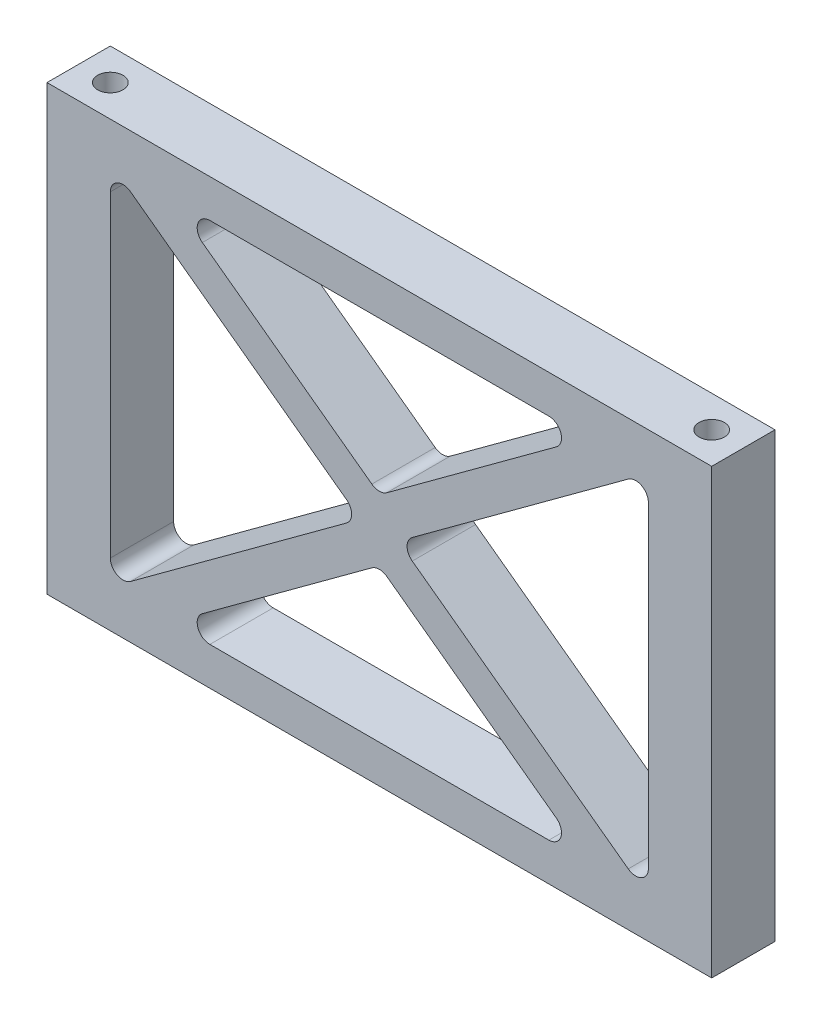
SolidWorks part; units mm, degrees
ref_plane "Ebene vorne" through (0, 0, 0) normal (0, 0, 1) x (1, 0, 0)
ref_plane "Ebene oben" through (0, 0, 0) normal (0, 1, 0) x (1, 0, 0)
ref_plane "Ebene rechts" through (0, 0, 0) normal (1, 0, 0) x (0, 0, -1)
sketch "Skizze1" plane through (0, 0, 0) normal (0, 0, 1) x (1, 0, 0)
  line L1 (0, 0) -> (105, 0)
  line L2 (0, 0) -> (0, 70)
  line L3 (0, 70) -> (105, 70)
  line L4 (105, 0) -> (105, 70)
  dimension "D1" = 105
  dimension "D2" = 70
extrude "Aufsatz-Linear austragen1" add sketch "Skizze1" along normal blind 10
sketch "Skizze2" plane through (0, 0, 10) normal (0, 0, 1) x (1, 0, 0)
  line L0 (10, 60.0503) -> (10, 9.9497)
  line L1 (52.5, 51.6277) -> (52.5, -7.4804) construction
  line L2 (13.1837, 61.6625) -> (47.3016, 36.6121)
  line L4 (51.3163, 40.7293) -> (24.5418, 60.3879)
  line L5 (25.7255, 64) -> (79.2745, 64)
  line L6 (105, 70) -> (0, 70) construction
  line L8 (0, 70) -> (0, 0) construction
  line L9 (-2.0593, 35) -> (95.2495, 35) construction
  line L10 (25.7255, 6) -> (79.2745, 6)
  line L11 (51.3163, 29.2707) -> (24.5418, 9.6121)
  line L12 (13.1837, 8.3375) -> (47.3016, 33.3879)
  line L13 (53.6837, 40.7293) -> (80.4582, 60.3879)
  line L14 (53.6837, 29.2707) -> (80.4582, 9.6121)
  line L15 (95, 60.0503) -> (95, 9.9497)
  line L16 (91.8163, 8.3375) -> (57.6984, 33.3879)
  line L17 (91.8163, 61.6625) -> (57.6984, 36.6121)
  line L18 (105, 0) -> (105, 70) construction
  arc A0 (95, 9.9497) -> (91.8163, 8.3375) centre (93, 9.9497) cw
  arc A1 (95, 60.0503) -> (91.8163, 61.6625) centre (93, 60.0503) ccw
  arc A2 (57.6984, 33.3879) -> (57.6984, 36.6121) centre (58.882, 35) cw
  arc A3 (80.4582, 9.6121) -> (79.2745, 6) centre (79.2745, 8) cw
  arc A4 (25.7255, 6) -> (24.5418, 9.6121) centre (25.7255, 8) cw
  arc A5 (51.3163, 29.2707) -> (53.6837, 29.2707) centre (52.5, 27.6586) cw
  arc A6 (80.4582, 60.3879) -> (79.2745, 64) centre (79.2745, 62) ccw
  arc A7 (51.3163, 40.7293) -> (53.6837, 40.7293) centre (52.5, 42.3414) ccw
  arc A8 (24.5418, 60.3879) -> (25.7255, 64) centre (25.7255, 62) cw
  arc A9 (47.3016, 36.6121) -> (47.3016, 33.3879) centre (46.118, 35) cw
  arc A10 (13.1837, 8.3375) -> (10, 9.9497) centre (12, 9.9497) cw
  arc A11 (10, 60.0503) -> (13.1837, 61.6625) centre (12, 60.0503) cw
  point P19 (10, 35)
  point P20 (52.5, 64)
  point P21 (52.5, 6)
  point P30 (95, 6)
  point P33 (95, 64)
  point P36 (55.5027, 35)
  point P39 (85.3778, 6)
  point P42 (19.6222, 6)
  point P45 (52.5, 30.1398)
  point P48 (85.3778, 64)
  point P51 (52.5, 39.8602)
  point P54 (19.6222, 64)
  point P57 (49.4973, 35)
  point P60 (10, 6)
  point P63 (10, 64)
  dimension "D5" = 2
  dimension "D1" = 6
  dimension "D2" = 6
  dimension "D3" = 10
  dimension "D4" = 10
extrude "Schnitt-Linear austragen1" cut sketch "Skizze2" against normal blind 10
sketch "Skizze3" plane through (0, 70, 0) normal (0, 1, 0) x (1, 0, 0)
  line L0 (105, -10) -> (105, 0) construction
  line L1 (0, -10) -> (0, 0) construction
  line L2 (105, -10) -> (0, -10) construction
  circle A0 centre (5, -5) radius 1.5
  circle A1 centre (100, -5) radius 1.5
  dimension "D1" = 3
  dimension "D2" = 3
  dimension "D3" = 5
  dimension "D4" = 5
  dimension "D5" = 5
  dimension "D6" = 5
extrude "Schnitt-Linear austragen2" cut sketch "Skizze3" against normal through all
sketch "Skizze4" plane through (0, 0, 0) normal (0, -1, 0) x (1, 0, 0)
  circle A0 centre (5, 5) radius 2
  circle A1 centre (100, 5) radius 2
  dimension "D1" = 4
  dimension "D2" = 4
extrude "Schnitt-Linear austragen3" cut sketch "Skizze4" against normal blind 6
sketch "Skizze5" plane through (0, 70, 0) normal (0, 1, 0) x (1, 0, 0)
  circle A0 centre (5, -5) radius 2
  circle A1 centre (100, -5) radius 2
  dimension "D1" = 4
  dimension "D2" = 4
extrude "Schnitt-Linear austragen4" cut sketch "Skizze5" against normal blind 6
